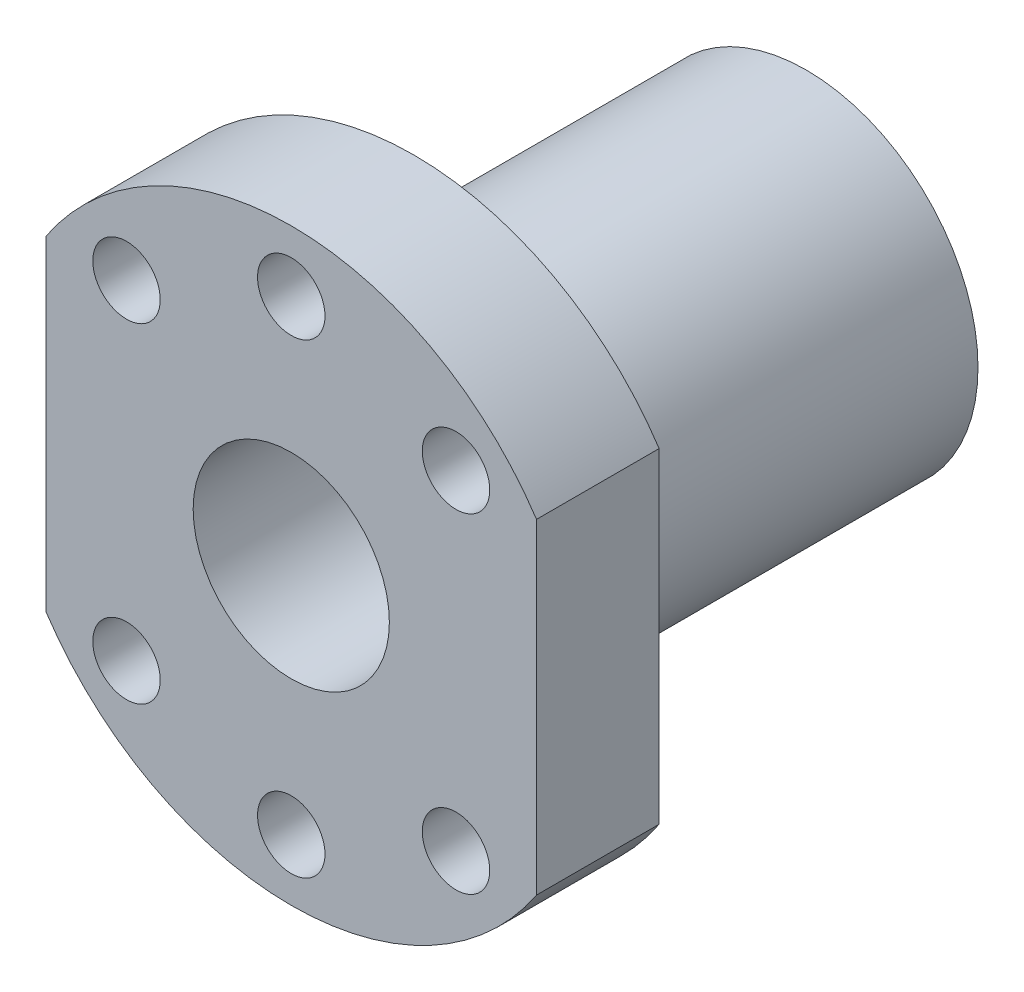
SolidWorks part; units mm, degrees
material "1060 Alloy"
ref_plane "Front Plane" through (0, 0, 0) normal (0, 0, 1) x (1, 0, 0)
ref_plane "Top Plane" through (0, 0, 0) normal (0, 1, 0) x (1, 0, 0)
ref_plane "Right Plane" through (0, 0, 0) normal (1, 0, 0) x (0, 0, -1)
sketch "Sketch1" plane through (0, 0, 0) normal (1, 0, 0) x (0, 0, -1)
  line L0 (-76.8751, 20.3432) -> (105.781, 20.3432) construction
  line L1 (-27.2282, 44.3432) -> (-17.2282, 44.3432)
  line L2 (-17.2282, 44.3432) -> (-17.2282, 34.3432)
  line L3 (-17.2282, 34.3432) -> (14.7718, 34.3432)
  line L4 (14.7718, 34.3432) -> (14.7718, 28.3432)
  line L5 (14.7718, 28.3432) -> (-27.2282, 28.3432)
  line L6 (-27.2282, 28.3432) -> (-27.2282, 44.3432)
  dimension "D1" = 8
  dimension "D2" = 10
  dimension "D3" = 42
  dimension "D4" = 24
  dimension "D5" = 14
revolve "Revolve1" add sketch "Sketch1" angle 360 about L0
sketch "Sketch2" plane through (0, 0, 27.2282) normal (0, 0, 1) x (1, 0, 0)
  line L2 (-20, 33.6097) -> (-20, 7.0767)
  line L3 (20, 33.6097) -> (20, 7.0767)
  arc A0 (-20, 33.6097) -> (-20, 7.0767) centre (0, 20.3432) ccw
  arc A1 (20, 7.0767) -> (20, 33.6097) centre (0, 20.3432) ccw
extrude "Extrude1" cut sketch "Sketch2" against normal blind 10
sketch "Sketch3" plane through (0, 0, 27.2282) normal (0, 0, 1) x (1, 0, 0)
  circle A1 centre (13.435, 33.7782) radius 2.75
  circle A2 centre (0, 39.3432) radius 2.75
  circle A3 centre (-13.435, 33.7782) radius 2.75
  circle A4 centre (-13.435, 6.9082) radius 2.75
  circle A5 centre (0, 1.3432) radius 2.75
  circle A6 centre (13.435, 6.9082) radius 2.75
extrude "Extrude2" cut sketch "Sketch3" against normal blind 10
